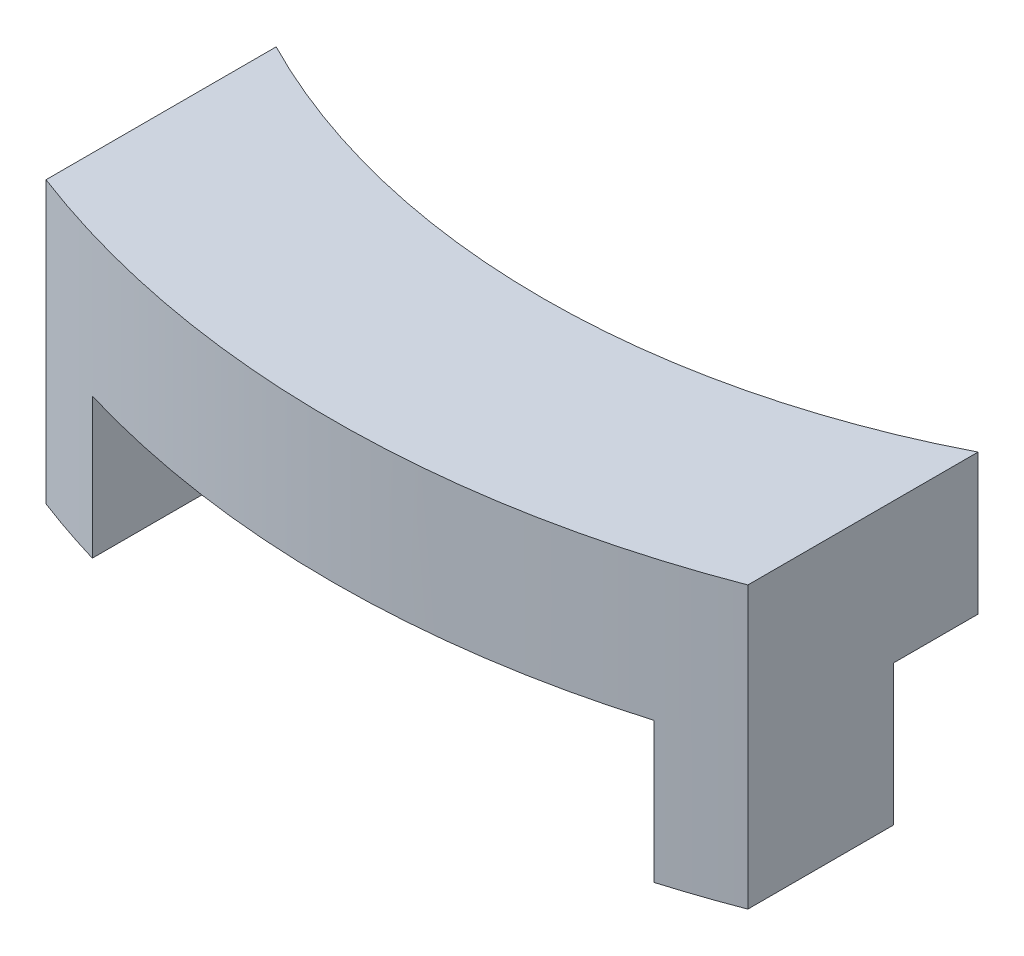
SolidWorks part; units mm, degrees
ref_plane "Front Plane" through (0, 0, 0) normal (0, 0, 1) x (1, 0, 0)
ref_plane "Top Plane" through (0, 0, 0) normal (0, 1, 0) x (1, 0, 0)
ref_plane "Right Plane" through (0, 0, 0) normal (1, 0, 0) x (0, 0, -1)
sketch "Sketch1" plane through (0, 0, 0) normal (0, 1, 0) x (1, 0, 0)
  line L0 (0, 0) -> (0, -11) construction
  line L1 (-5, -9.798) -> (-5, -13.0767)
  line L2 (5, -9.798) -> (5, -13.0767)
  arc A0 (-5, -13.0767) -> (5, -13.0767) centre (0, 0) ccw
  arc A1 (-5, -9.798) -> (5, -9.798) centre (0, 0) ccw
  dimension "D1" = 22
  dimension "D2" = 28
  dimension "D3" = 5
  dimension "D4" = 5
extrude "Boss-Extrude1" add sketch "Sketch1" along normal blind 2
sketch "Sketch3" plane through (0, 0, 0) normal (0, -1, 0) x (1, 0, 0)
  line L0 (0, 14) -> (0, 11) construction
  line L1 (5, 13.0767) -> (5, 9.798) construction
  line L2 (-5, 9.798) -> (-5, 13.0767) construction
  line L3 (5, 13.0767) -> (5, 11)
  line L4 (-5, 11) -> (-5, 13.0767)
  line L5 (-4, 13.4164) -> (-4, 11)
  line L6 (4, 13.4164) -> (4, 11)
  line L7 (-5, 11) -> (-4, 11)
  line L8 (4, 11) -> (5, 11)
  arc A0 (5, 13.0767) -> (-5, 13.0767) centre (0, 0) ccw construction
  arc A1 (5, 9.798) -> (-5, 9.798) centre (0, 0) ccw construction
  arc A3 (5, 13.0767) -> (4, 13.4164) centre (0, 0) ccw
  arc A4 (-4, 13.4164) -> (-5, 13.0767) centre (0, 0) ccw
  dimension "D1" = 1
  dimension "D2" = 1
  dimension "D3" = 11
extrude "Boss-Extrude2" add sketch "Sketch3" along normal blind 2
